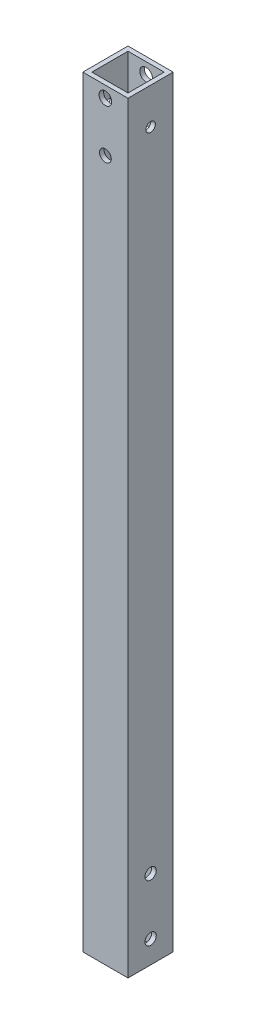
SolidWorks part; units mm, degrees
material "Gerais  - 6061-T6"
ref_plane "Plano frontal" through (0, 0, 0) normal (0, 0, 1) x (1, 0, 0)
ref_plane "Plano superior" through (0, 0, 0) normal (0, 1, 0) x (1, 0, 0)
ref_plane "Plano direito" through (0, 0, 0) normal (1, 0, 0) x (0, 0, -1)
sketch "Esboço1" plane through (0, 0, 0) normal (0, 1, 0) x (1, 0, 0)
  line L1 (0, 0) -> (20, 0)
  line L2 (0, 0) -> (0, 20)
  line L3 (0, 20) -> (20, 20)
  line L4 (20, 0) -> (20, 20)
  dimension "D1" = 20
extrude "Extrusão-Fina1" add sketch "Esboço1" along normal blind 337 thin thin type one direction reverse wall 2
sketch "Esboço2" plane through (0, 0, 0) normal (-1, 0, 0) x (0, 0, 1)
  circle A0 centre (-10, 35) radius 2.5
  circle A1 centre (-10, 10) radius 2.5
extrude "Corte-extrusão1" cut sketch "Esboço2" against normal through all
sketch "Esboço3" plane through (0, 0, -20) normal (0, 0, -1) x (-1, 0, 0)
  circle A2 centre (-10, 310) radius 2.6
  circle A3 centre (-10, 332) radius 2.8
extrude "Corte-extrusão2" cut sketch "Esboço3" against normal through all
sketch "Esboço4" plane through (20, 0, 0) normal (1, 0, 0) x (0, 0, -1)
  line L0 (0, 337) -> (20, 337) construction
  circle A0 centre (10, 321) radius 2.1
  point P3 (10, 337)
  dimension "D1" = 4.2
  dimension "D2" = 16
extrude "Corte-extrusão3" cut sketch "Esboço4" against normal through all
